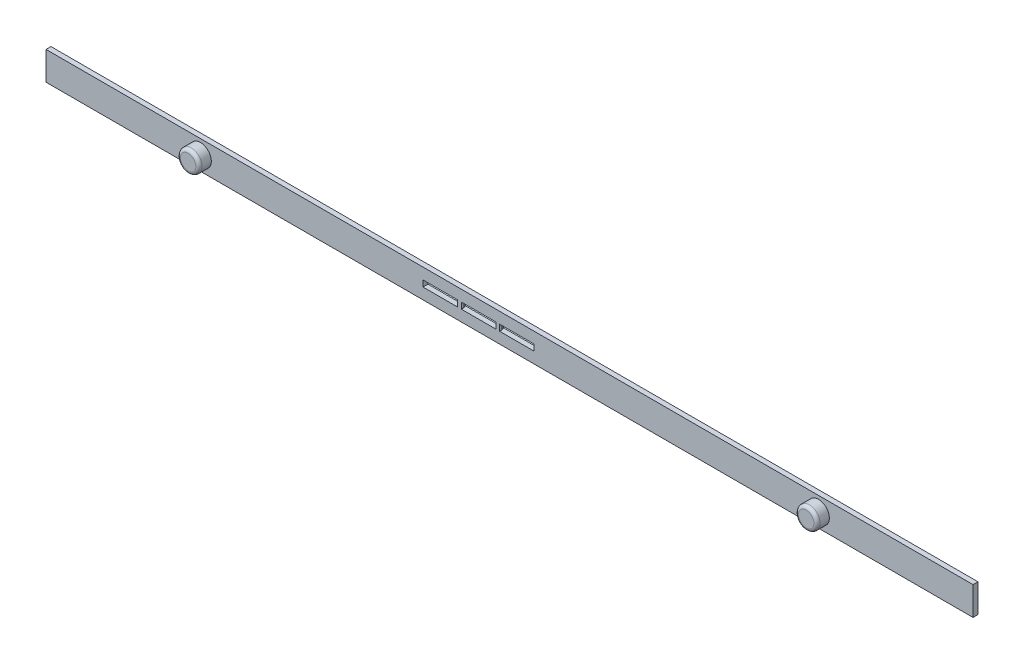
SolidWorks part; units mm, degrees
ref_plane "Přední rovina" through (0, 0, 0) normal (0, 0, 1) x (1, 0, 0)
ref_plane "Horní rovina" through (0, 0, 0) normal (0, 1, 0) x (1, 0, 0)
ref_plane "Pravá rovina" through (0, 0, 0) normal (1, 0, 0) x (0, 0, -1)
sketch "Skica2" plane through (0, 0, 0) normal (0, 0, 1) x (1, 0, 0)
  line L1 (-75, 2.3) -> (75, 2.3)
  line L2 (-75, 2.3) -> (-75, -2.3)
  line L3 (-75, -2.3) -> (75, -2.3)
  line L4 (75, 2.3) -> (75, -2.3)
  line L5 (-75, 2.3) -> (75, -2.3) construction
  line L6 (-75, -2.3) -> (75, 2.3) construction
  line L7 (4, 0.5) -> (-14, 0.5)
  line L8 (4, 0.5) -> (4, -0.5)
  line L9 (4, -0.5) -> (-14, -0.5)
  line L10 (-14, 0.5) -> (-14, -0.5)
  line L11 (4, 0.5) -> (-14, -0.5) construction
  line L12 (4, -0.5) -> (-14, 0.5) construction
  point P0 (0, 0)
  point P5 (-5, 0)
  dimension "D1" = 4.6
  dimension "D2" = 150
  dimension "D3" = 1
  dimension "D4" = 18
  dimension "D5" = 61
extrude "Přidat vysunutím2" add sketch "Skica2" along normal blind 0.8
sketch "Skica3" plane through (0, 0, 0.8) normal (0, 0, 1) x (1, 0, 0)
  line L0 (-75, 2.3) -> (-75, -2.3) construction
  line L1 (75, -2.3) -> (75, 2.3) construction
  line L2 (75, 2.3) -> (-75, 2.3) construction
  line L3 (-75, -2.3) -> (75, -2.3) construction
  circle A0 centre (-50, 0) radius 1.75
  circle A1 centre (50, 0) radius 1.75
  dimension "D1" = 3.5
  dimension "D3" = 3.5
  dimension "D2" = 25
  dimension "D4" = 25
  dimension "D5" = 2.3
  dimension "D6" = 2.3
extrude "Přidat vysunutím3" add sketch "Skica3" along normal blind 2
fillet "Zaoblit1" radius 0.5 2 edges at (51.75, 0, 2.8) (-48.25, 0, 2.8)
sketch "Skica4" plane through (0, 0, 0) normal (0, 0, -1) x (-1, 0, 0)
  line L0 (14, -0.5) -> (-4, -0.5) construction
  line L1 (2.2, 0.5) -> (1.6, 0.5)
  line L2 (2.2, 0.5) -> (2.2, -0.5)
  line L3 (2.2, -0.5) -> (1.6, -0.5)
  line L4 (1.6, 0.5) -> (1.6, -0.5)
  line L5 (2.2, 0.5) -> (1.6, -0.5) construction
  line L6 (2.2, -0.5) -> (1.6, 0.5) construction
  line L7 (-4, -0.5) -> (-4, 0.5) construction
  line L8 (14, 0.5) -> (14, -0.5) construction
  line L9 (7.8, 0.5) -> (8.4, 0.5)
  line L10 (7.8, 0.5) -> (7.8, -0.5)
  line L11 (7.8, -0.5) -> (8.4, -0.5)
  line L12 (8.4, 0.5) -> (8.4, -0.5)
  line L13 (7.8, 0.5) -> (8.4, -0.5) construction
  line L14 (7.8, -0.5) -> (8.4, 0.5) construction
  point P0 (1.9, 0)
  point P7 (1.6, 0)
  point P10 (8.1, 0)
  dimension "D1" = 1
  dimension "D2" = 0.6
  dimension "D3" = 5.6
  dimension "D4" = 0.6
  dimension "D5" = 5.6
  dimension "D6" = 5.6
extrude "Přidat vysunutím4" add sketch "Skica4" against normal blind 0.8
chamfer "Zkosení1" distance 0.4 angle 20 4 edges at (-7.8, 0, 0) (-8.4, 0, 0) (-2.2, 0, 0) (-1.6, 0, 0)
